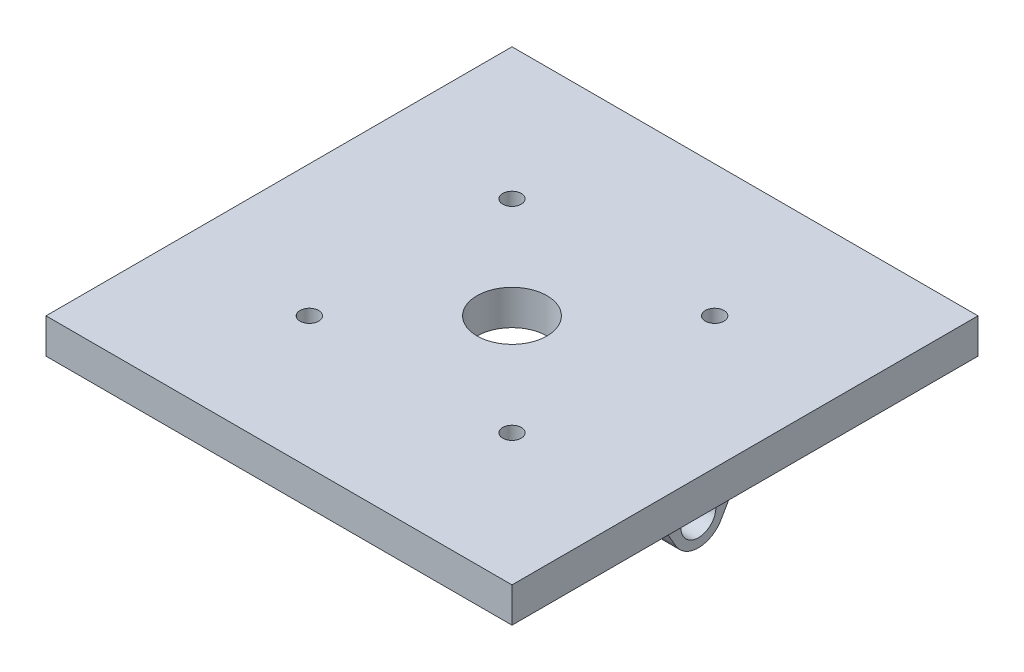
SolidWorks part; units mm, degrees
ref_plane "Plano frontal" through (0, 0, 0) normal (0, 0, 1) x (1, 0, 0)
ref_plane "Plano superior" through (0, 0, 0) normal (0, 1, 0) x (1, 0, 0)
ref_plane "Plano direito" through (0, 0, 0) normal (1, 0, 0) x (0, 0, -1)
sketch "Esboço1" plane through (0, 0, 0) normal (0, 1, 0) x (1, 0, 0)
  line L1 (-200, -200) -> (200, -200)
  line L2 (-200, -200) -> (-200, 200)
  line L3 (-200, 200) -> (200, 200)
  line L4 (200, -200) -> (200, 200)
  line L5 (-200, -200) -> (200, 200) construction
  line L6 (-200, 200) -> (200, -200) construction
  circle A0 centre (0, 0) radius 30
  point P0 (0, 0)
  dimension "D2" = 60
  dimension "D1" = 400
extrude "Ressalto-extrusão1" add sketch "Esboço1" along normal blind 30
sketch "Esboço2" plane through (0, 0, 0) normal (1, 0, 0) x (0, 0, -1)
  line L0 (0, 0) -> (0, 30) construction
  line L1 (-200, 0) -> (200, 0) construction
  line L2 (-200, 30) -> (200, 30) construction
  line L3 (-19.4856, -51.25) -> (-44.7446, -7.5)
  line L4 (0, -40) -> (0, 0) construction
  line L5 (-57.735, 0) -> (57.735, 0)
  line L6 (19.4856, -51.25) -> (44.7446, -7.5)
  arc A0 (44.7446, -7.5) -> (57.735, 0) centre (57.735, -15) cw
  arc A1 (-44.7446, -7.5) -> (-57.735, 0) centre (-57.735, -15) ccw
  arc A2 (-19.4856, -51.25) -> (19.4856, -51.25) centre (0, -40) ccw
  circle A3 centre (0, -40) radius 15
  dimension "D1" = 30
  dimension "D2" = 45
  dimension "D6" = 30
  dimension "D4" = 40
  dimension "D5" = 60
extrude "Ressalto-extrusão2" add sketch "Esboço2" along normal blind 30 from offset 130
mirror "Espelhar1" about plane through (0, 0, 0) normal (1, 0, 0) of "Ressalto-extrusão2"
sketch "Esboço3" plane through (0, 30, 0) normal (0, 1, 0) x (1, 0, 0)
  line L0 (0, 0) -> (0, 200) construction
  line L1 (200, 200) -> (-200, 200) construction
  line L2 (0, 0) -> (200, 0) construction
  line L3 (200, -200) -> (200, 200) construction
  circle A0 centre (-86.974, 86.974) radius 8
  circle A1 centre (86.974, 86.974) radius 8
  circle A2 centre (86.974, -86.974) radius 8
  circle A3 centre (-86.974, -86.974) radius 8
  dimension "D1" = 16
extrude "Corte-extrusão1" cut sketch "Esboço3" against normal through all
sketch "Esboço4" [suppressed] plane through (0, 0, 0) normal (1, 0, 0) x (0, 0, -1)
  line L0 (-15, 0) -> (15, 0)
  line L2 (15, 0) -> (15, 12.5)
  line L3 (15, 12.5) -> (-15, 12.5)
  line L4 (-15, 0) -> (-15, 12.5)
  line L5 (0, 0) -> (-15, 12.5) construction
  line L6 (15, 12.5) -> (0, 0) construction
  point P0 (0, 0)
  dimension "D1" = 12.5
  dimension "D2" = 30
extrude "Corte-extrusão2" [suppressed] cut sketch "Esboço4" against normal through all both and the other way through all
equation "\"D3@Esboço3\"=\"D2@Esboço3\""
